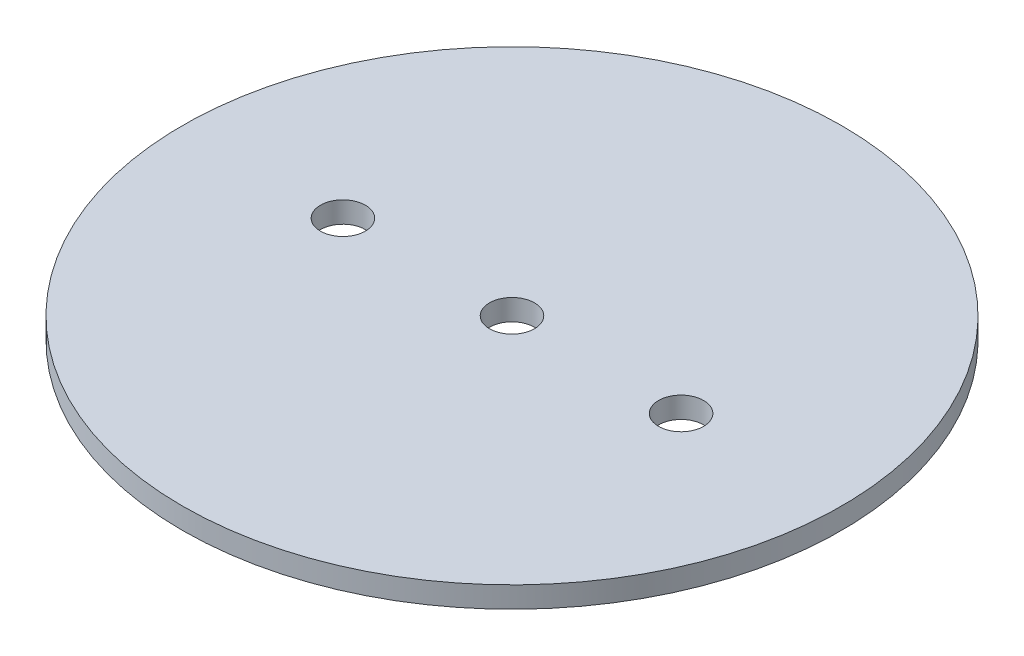
SolidWorks part; units mm, degrees
material "A-Glass Fiber"
ref_plane "Front Plane" through (0, 0, 0) normal (0, 0, 1) x (1, 0, 0)
ref_plane "Top Plane" through (0, 0, 0) normal (0, 1, 0) x (1, 0, 0)
ref_plane "Right Plane" through (0, 0, 0) normal (1, 0, 0) x (0, 0, -1)
sketch "Sketch1" plane through (0, 0, 0) normal (0, 1, 0) x (1, 0, 0)
  circle A0 centre (0, 0) radius 49.5046
  dimension "D1" = 99.0092
extrude "Boss-Extrude1" add sketch "Sketch1" along normal blind 3.175
sketch "Sketch3" plane through (0, 0, 0) normal (0, -1, 0) x (1, 0, 0)
  line L0 (-25.4, 0) -> (25.4, 0) construction
  point P2 (0, 0)
  dimension "D1" = 25.4
sketch "Sketch4" plane through (0, 0, 0) normal (0, -1, 0) x (-1, 0, 0)
  point P0 (-25.4, 0)
  point P3 (0, 0)
  point P6 (25.4, 0)
hole_wizard "1/4 Clearance Hole1" positions "Sketch4" profile "Sketch5" hole size "1/4" standard "ANSI Inch" end condition through all
sketch "Sketch5" plane through (25.4, 0, 0) normal (1, 0, 0) x (0, 0, -1)
  line L0 (0, 0) -> (0, 3.175)
  line L1 (0, 3.175) -> (3.3782, 3.175)
  line L2 (3.3782, 3.175) -> (3.3782, 0)
  line L5 (3.3782, 0) -> (0, 0)
  line L11 (0, -6.35) -> (0, 107.95) construction
  dimension "Thru Hole Dia." = 6.7564
  dimension "Thru Hole Depth" = 3.175
